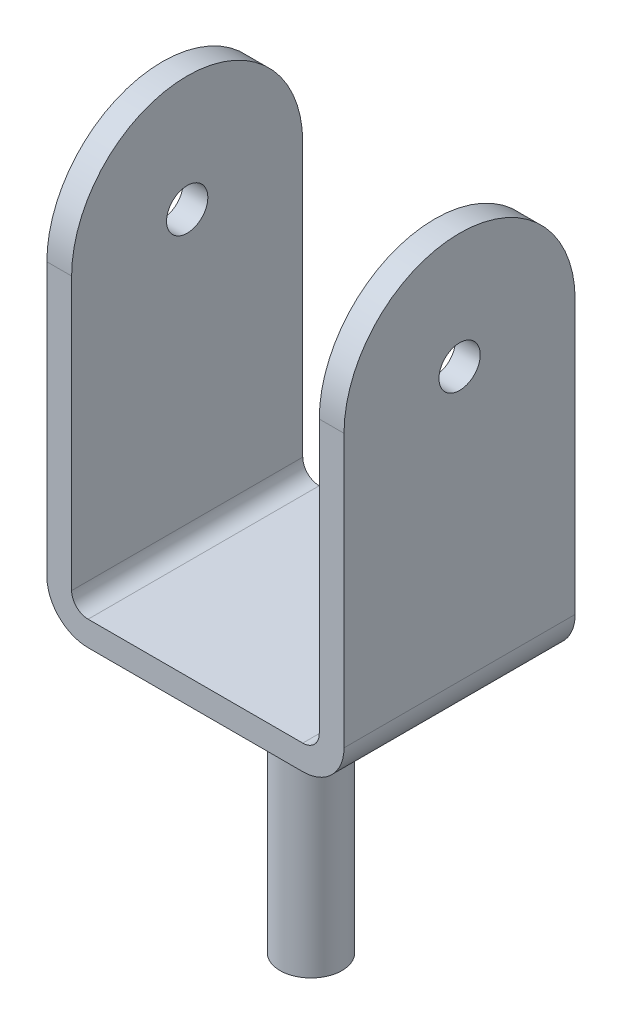
SolidWorks part; units mm, degrees
ref_plane "Front Plane" through (0, 0, 0) normal (0, 0, 1) x (1, 0, 0)
ref_plane "Top Plane" through (0, 0, 0) normal (0, 1, 0) x (1, 0, 0)
ref_plane "Right Plane" through (0, 0, 0) normal (1, 0, 0) x (0, 0, -1)
sketch "Sketch1" plane through (0, 0, 0) normal (0, 0, 1) x (1, 0, 0)
  line L0 (-130, 0) -> (130, 0)
  line L1 (-180, 50) -> (-180, 520)
  line L2 (-180, 520) -> (-150, 520)
  line L3 (-150, 520) -> (-150, 50)
  line L4 (-130, 30) -> (130, 30)
  line L5 (0, 699.4487) -> (0, -329.1741) construction
  line L6 (150, 520) -> (150, 50)
  line L7 (180, 520) -> (150, 520)
  line L8 (180, 50) -> (180, 520)
  arc A0 (-130, 0) -> (-180, 50) centre (-130, 50) cw
  arc A1 (-150, 50) -> (-130, 30) centre (-130, 50) ccw
  arc A2 (150, 50) -> (130, 30) centre (130, 50) cw
  arc A3 (130, 0) -> (180, 50) centre (130, 50) ccw
  point P12 (0, 0)
  point P16 (0, 30)
  dimension "D3" = 20
  dimension "D1" = 360
  dimension "D2" = 30
  dimension "D6" = 520
extrude "Boss-Extrude1" add sketch "Sketch1" along normal blind 280
sketch "Sketch2" plane through (-180, 0, 0) normal (-1, 0, 0) x (0, 0, 1)
  line L0 (140, 571.5016) -> (140, -36.8806) construction
  line L1 (-89.3765, 380) -> (369.3765, 380) construction
  line L2 (0, 520) -> (0, 50) construction
  line L3 (280, 520) -> (0, 520) construction
  line L4 (280, 520) -> (280, 50) construction
  arc A0 (0, 380) -> (280, 380) centre (140, 380) cw
  circle A2 centre (140, 380) radius 25
  point P4 (140, 380)
  line M3 (0, 520) -> (0, 50)
  line M5 (280, 50) -> (280, 520)
  line M6 (280, 520) -> (0, 520)
  dimension "D3" = 140
  dimension "D4" = 50
  dimension "D1" = 140
  dimension "D2" = 140
extrude "Cut-Extrude3" cut sketch "Sketch2" against normal blind 399 and the other way through all contours A0 M6 M5 | A0 M3 M6 | A2
sketch "Sketch4" plane through (0, 0, 0) normal (0, -1, 0) x (1, 0, 0)
  line L0 (0, 313.1693) -> (0, -33.1693) construction
  line L1 (-244.1844, 140) -> (244.1844, 140) construction
  line L3 (-130, 280) -> (130, 280) construction
  circle A0 centre (0, 140) radius 37.5
  point P5 (0, 140)
  point P6 (0, 140)
  dimension "D2" = 75
  dimension "D1" = 140
extrude "Boss-Extrude2" add sketch "Sketch4" along normal blind 325
